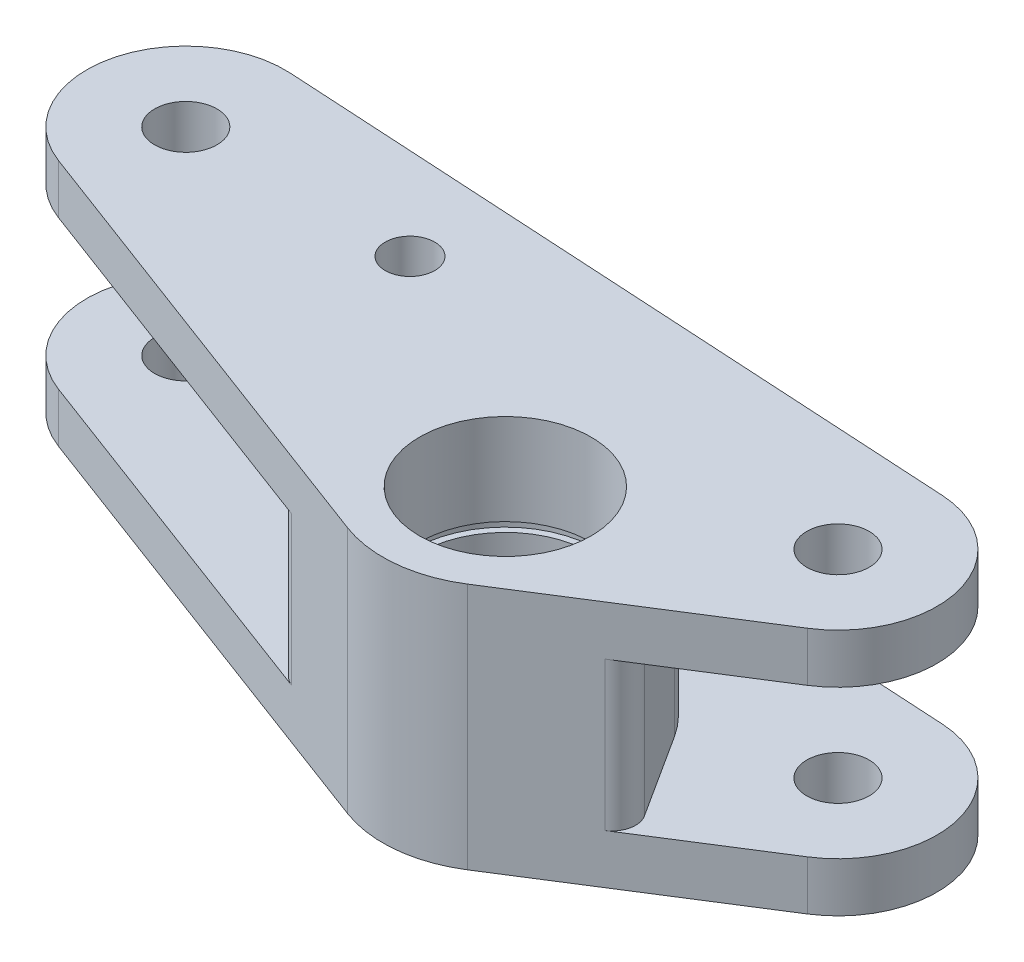
SolidWorks part; units mm, degrees
ref_plane "Front Plane" through (0, 0, 0) normal (0, 0, 1) x (1, 0, 0)
ref_plane "Top Plane" through (0, 0, 0) normal (0, 1, 0) x (1, 0, 0)
ref_plane "Right Plane" through (0, 0, 0) normal (1, 0, 0) x (0, 0, -1)
sketch "Sketch2" plane through (0, 0, 0) normal (0, 1, 0) x (1, 0, 0)
  line L13 (16.7801, 23.2734) -> (76.1691, 0.9994)
  line L14 (90.086, 2.4332) -> (116.7953, 19.3333)
  line L15 (21.9682, 47.8437) -> (110.7331, 42.7445)
  circle A3 centre (81.6859, 15.7088) radius 9
  circle A37 centre (110.0047, 30.0654) radius 4
  circle A45 centre (21.2399, 35.1646) radius 4
  circle A47 centre (21.2399, 35.1646) radius 1
  arc A53 (76.1691, 0.9994) -> (90.086, 2.4332) centre (81.6859, 15.7088) ccw
  arc A54 (116.7953, 19.3333) -> (110.7331, 42.7445) centre (110.0047, 30.0654) ccw
  arc A55 (21.9682, 47.8437) -> (16.7801, 23.2734) centre (21.2399, 35.1646) ccw
  circle A60 centre (50, 35.1646) radius 3.175
  point P1 (21.2399, 35.1646)
  point P4 (81.6859, 15.7088)
  point P6 (25.4, 57.15)
  point P8 (125.2248, 40.843)
  point P9 (81.6859, -2.0061)
  point P10 (81.6859, 64.2682)
  point P16 (3.598, 40.843)
  point P17 (49.5281, 49.4258)
  point P25 (50, 35.1646)
extrude "Boss-Extrude1" add sketch "Sketch2" against normal blind 31.75
ref_plane "Plane1" through (0, -6.35, 0) normal (0, 1, 0) x (1, 0, 0)
sketch "Sketch3" plane through (0, -6.35, 0) normal (0, 1, 0) x (1, 0, 0)
  line L1 (94.91, 24.1876) -> (101.8111, 13.4243)
  line L2 (71.4298, 27.6075) -> (63.7413, 20.9804)
  line L4 (62.7, 18.7081) -> (62.7, 8.1301)
  line L8 (64.6467, 5.321) -> (8.5399, 20.9804)
  line L9 (8.5399, 20.9804) -> (8.5399, 47.8646)
  line L10 (8.5399, 47.8646) -> (123.8505, 47.8646)
  line L11 (123.8505, 47.8646) -> (124.8965, 9.2699)
  line L12 (124.8965, 9.2699) -> (100.8896, 9.2699)
  arc A0 (94.91, 24.1876) -> (71.4298, 27.6075) centre (81.6859, 15.7088) ccw
  arc A5 (100.8896, 9.2699) -> (101.8111, 13.4243) centre (99.2856, 11.8051) ccw
  arc A6 (63.7413, 20.9804) -> (62.7, 18.7081) centre (65.7, 18.7081) ccw
  arc A8 (64.6467, 5.321) -> (62.7, 8.1301) centre (65.7, 8.1301) cw
  dimension "D1" = 3
  dimension "D2" = 3
extrude "Cut-Extrude7" cut sketch "Sketch3" against normal blind 19.05
sketch "Sketch4" plane through (0, 0, 0) normal (0, 1, 0) x (1, 0, 0)
  circle A0 centre (81.6859, 15.7088) radius 11
extrude "Cut-Extrude8" cut sketch "Sketch4" against normal blind 18.875
ref_plane "Plane2" through (0, -12.875, 0) normal (0, 1, 0) x (1, 0, 0)
sketch "Sketch5" plane through (0, -12.875, 0) normal (0, 1, 0) x (1, 0, 0)
  circle A0 centre (81.6859, 15.7088) radius 11.825
  point P0 (81.6859, 15.7088)
extrude "Cut-Extrude9" cut sketch "Sketch5" along normal blind 1.2
